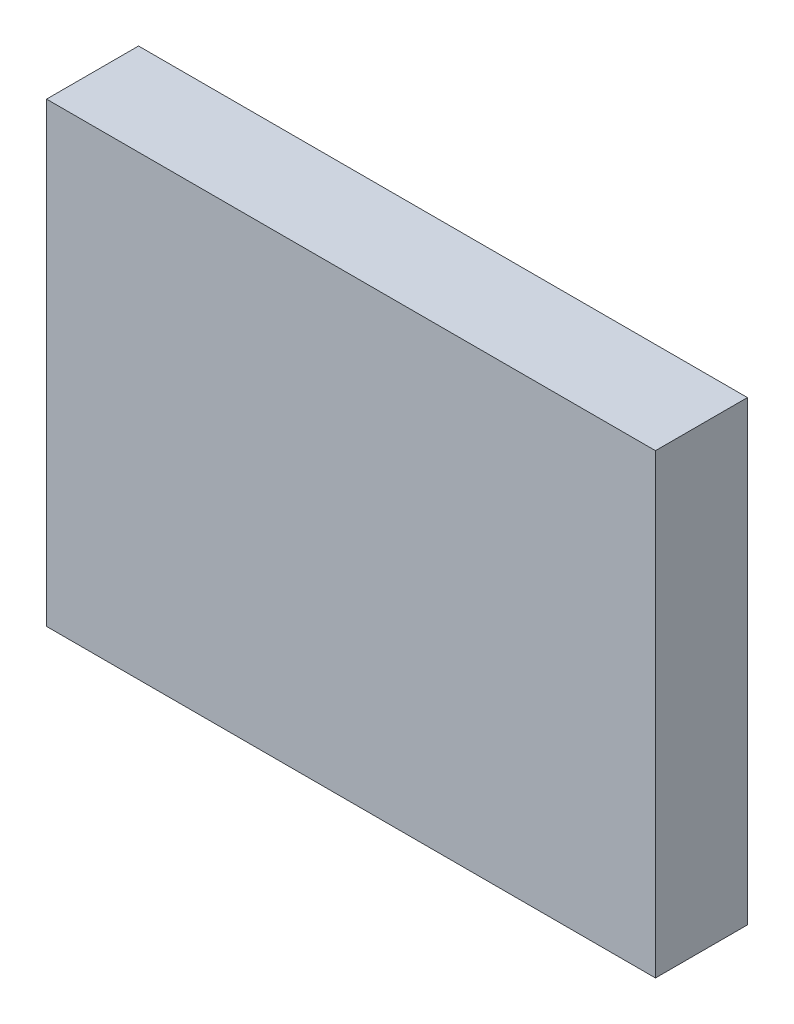
SolidWorks part; units mm, degrees
ref_plane "Front Plane" through (0, 0, 0) normal (0, 0, 1) x (1, 0, 0)
ref_plane "Top Plane" through (0, 0, 0) normal (0, 1, 0) x (1, 0, 0)
ref_plane "Right Plane" through (0, 0, 0) normal (1, 0, 0) x (0, 0, -1)
sketch "Sketch1" plane through (0, 0, 0) normal (0, 0, 1) x (1, 0, 0)
  line L1 (-2.4, -1.8) -> (2.4, -1.8)
  line L2 (-2.4, -1.8) -> (-2.4, 1.8)
  line L3 (-2.4, 1.8) -> (2.4, 1.8)
  line L4 (2.4, -1.8) -> (2.4, 1.8)
  line L5 (-2.4, -1.8) -> (2.4, 1.8) construction
  line L6 (-2.4, 1.8) -> (2.4, -1.8) construction
  point P0 (0, 0)
  dimension "D1" = 3.6
  dimension "D2" = 4.8
extrude "Boss-Extrude1" add sketch "Sketch1" along normal blind 0.725
